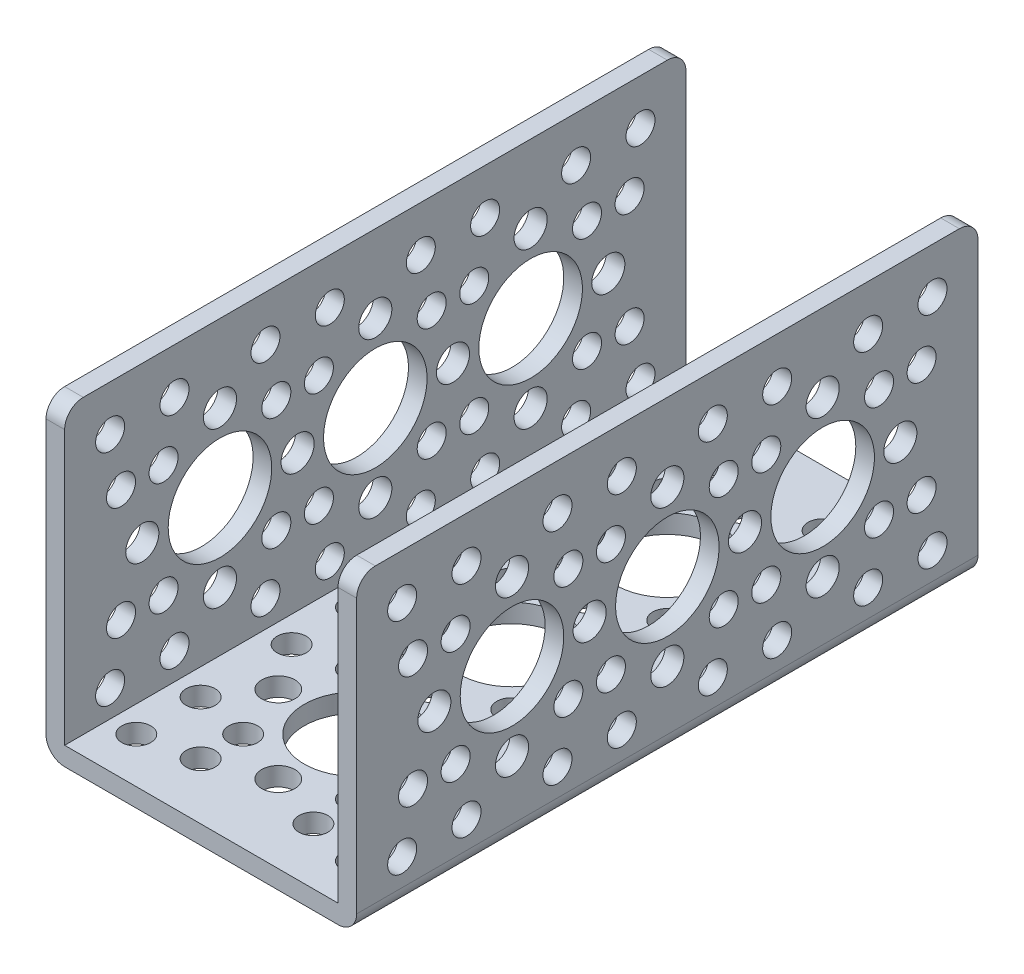
SolidWorks part; units mm, degrees
ref_plane "Front Plane" through (0, 0, 0) normal (0, 0, 1) x (1, 0, 0)
ref_plane "Top Plane" through (0, 0, 0) normal (0, 1, 0) x (1, 0, 0)
ref_plane "Right Plane" through (0, 0, 0) normal (1, 0, 0) x (0, 0, -1)
sketch "Sketch1" plane through (0, 0, 0) normal (0, 0, 1) x (1, 0, 0)
  line L1 (0, 0) -> (38.1, 0)
  line L2 (0, 0) -> (0, 38.1)
  line L4 (38.1, 0) -> (38.1, 38.1)
extrude "Extrude-Thin1" add sketch "Sketch1" along normal blind 76.2 thin thin type one direction wall 2.286
sketch "Sketch3" plane through (0, 0, 0) normal (0, -1, 0) x (1, 0, 0)
  line L0 (38.1, 0) -> (0, 0) construction
  circle B0 centre (19.05, 19.0584) radius 6.35
  circle B1 centre (19.05, 9.5334) radius 2.032
  circle B2 centre (9.525, 19.0584) radius 2.032
  circle B3 centre (19.05, 28.5834) radius 2.032
  circle B4 centre (28.575, 19.0584) radius 2.032
  circle B5 centre (12.1352, 25.9732) radius 1.778
  circle B6 centre (5.5796, 32.5288) radius 1.778
  circle B7 centre (25.9648, 25.9732) radius 1.778
  circle B8 centre (32.5204, 32.5288) radius 1.778
  circle B9 centre (25.9648, 12.1436) radius 1.778
  circle B10 centre (32.5204, 5.588) radius 1.778
  circle B11 centre (12.1352, 12.1436) radius 1.778
  circle B12 centre (5.5796, 5.588) radius 1.778
  circle B13 centre (12.1352, 31.1936) radius 1.778
  circle B14 centre (25.9648, 31.1936) radius 1.778
  circle B15 centre (25.9648, 6.9232) radius 1.778
  circle B16 centre (12.1352, 6.9232) radius 1.778
  circle B17 centre (32.5204, 13.4788) radius 1.778
  circle B18 centre (5.5796, 13.4788) radius 1.778
  circle B19 centre (5.5796, 24.638) radius 1.778
  circle B20 centre (32.5204, 24.638) radius 1.778
  circle B21 centre (18.9713, 38.1084) radius 6.35
  circle B22 centre (9.4463, 38.1084) radius 2.032
  circle B23 centre (28.4963, 38.1084) radius 2.032
  circle B24 centre (18.9713, 57.1584) radius 6.35
  circle B25 centre (18.9713, 47.6334) radius 2.032
  circle B26 centre (9.4463, 57.1584) radius 2.032
  circle B27 centre (18.9713, 66.6834) radius 2.032
  circle B28 centre (28.4963, 57.1584) radius 2.032
  circle B29 centre (12.0565, 64.0732) radius 1.778
  circle B30 centre (5.5009, 70.6288) radius 1.778
  circle B31 centre (25.8861, 64.0732) radius 1.778
  circle B32 centre (32.4417, 70.6288) radius 1.778
  circle B33 centre (25.8861, 50.2436) radius 1.778
  circle B34 centre (32.4417, 43.688) radius 1.778
  circle B35 centre (12.0565, 50.2436) radius 1.778
  circle B36 centre (5.5009, 43.688) radius 1.778
  circle B37 centre (12.0565, 69.2936) radius 1.778
  circle B38 centre (25.8861, 69.2936) radius 1.778
  circle B39 centre (25.8861, 45.0232) radius 1.778
  circle B40 centre (12.0565, 45.0232) radius 1.778
  circle B41 centre (32.4417, 51.5788) radius 1.778
  circle B42 centre (5.5009, 51.5788) radius 1.778
  circle B43 centre (5.5009, 62.738) radius 1.778
  circle B44 centre (32.4417, 62.738) radius 1.778
  dimension "D1" = 19.05
  dimension "D2" = 38.1
  dimension "D3" = 5.588
sketch_block_instance "actobotics hole pattern-2"
sketch_block "actobotics hole pattern" parameters "D1"=12.7, "D3"=4.064, "D6"=3.556, "D7"=3.556, "D2"=9.525, "D4"=19.05, "D5"=9.779
sketch_block_instance "Actobotics hole pattern c-6"
sketch_block "Actobotics hole pattern c" parameters "D1"=12.7, "D4"=4.064, "D2"=19.05, "D3"=9.525
sketch_block_instance "actobotics hole pattern-1"
extrude "Cut-Extrude1" cut sketch "Sketch3" against normal up to next (2.286 mm away)
sketch "Sketch4" plane through (0, 0, 0) normal (-1, 0, 0) x (0, 0, 1)
  line L0 (0, 38.1) -> (76.2, 0) construction
  line L2 (76.2, 38.1) -> (0, 0) construction
  line L3 (76.2, 0) -> (76.2, 38.1) construction
  circle B0 centre (38.1, 19.05) radius 6.35
  circle B1 centre (38.1, 9.525) radius 2.032
  circle B2 centre (38.1, 28.575) radius 2.032
  circle B3 centre (19.05, 19.05) radius 6.35
  circle B4 centre (28.575, 19.05) radius 2.032
  circle B5 centre (19.05, 9.525) radius 2.032
  circle B6 centre (9.525, 19.05) radius 2.032
  circle B7 centre (19.05, 28.575) radius 2.032
  circle B8 centre (12.1352, 12.1352) radius 1.778
  circle B9 centre (5.5796, 5.5796) radius 1.778
  circle B10 centre (12.1352, 25.9648) radius 1.778
  circle B11 centre (5.5796, 32.5204) radius 1.778
  circle B12 centre (25.9648, 25.9648) radius 1.778
  circle B13 centre (32.5204, 32.5204) radius 1.778
  circle B14 centre (25.9648, 12.1352) radius 1.778
  circle B15 centre (32.5204, 5.5796) radius 1.778
  circle B16 centre (6.9148, 12.1352) radius 1.778
  circle B17 centre (6.9148, 25.9648) radius 1.778
  circle B18 centre (31.1852, 25.9648) radius 1.778
  circle B19 centre (31.1852, 12.1352) radius 1.778
  circle B20 centre (24.6296, 32.5204) radius 1.778
  circle B21 centre (24.6296, 5.5796) radius 1.778
  circle B22 centre (13.4704, 5.5796) radius 1.778
  circle B23 centre (13.4704, 32.5204) radius 1.778
  circle B24 centre (57.15, 19.05) radius 6.35
  circle B25 centre (66.675, 19.05) radius 2.032
  circle B26 centre (57.15, 9.525) radius 2.032
  circle B27 centre (47.625, 19.05) radius 2.032
  circle B28 centre (57.15, 28.575) radius 2.032
  circle B29 centre (50.2352, 12.1352) radius 1.778
  circle B30 centre (43.6796, 5.5796) radius 1.778
  circle B31 centre (50.2352, 25.9648) radius 1.778
  circle B32 centre (43.6796, 32.5204) radius 1.778
  circle B33 centre (64.0648, 25.9648) radius 1.778
  circle B34 centre (70.6204, 32.5204) radius 1.778
  circle B35 centre (64.0648, 12.1352) radius 1.778
  circle B36 centre (70.6204, 5.5796) radius 1.778
  circle B37 centre (45.0148, 12.1352) radius 1.778
  circle B38 centre (45.0148, 25.9648) radius 1.778
  circle B39 centre (69.2852, 25.9648) radius 1.778
  circle B40 centre (69.2852, 12.1352) radius 1.778
  circle B41 centre (62.7296, 32.5204) radius 1.778
  circle B42 centre (62.7296, 5.5796) radius 1.778
  circle B43 centre (51.5704, 5.5796) radius 1.778
  circle B44 centre (51.5704, 32.5204) radius 1.778
  dimension "D1" = 19.05
  dimension "D2" = 38.1
  dimension "D3" = 5.5796
sketch_block_instance "Actobotics hole pattern c-7"
sketch_block_instance "actobotics hole pattern-6"
sketch_block_instance "actobotics hole pattern-7"
extrude "Cut-Extrude2" cut sketch "Sketch4" against normal through all
fillet "Fillet1" radius 2.286 6 edges at (1.143, 38.1, 76.2) (36.957, 38.1, 76.2) (36.957, 38.1, 0) (1.143, 38.1, 0) (38.1, 0, 38.1) (0, 0, 38.1)
